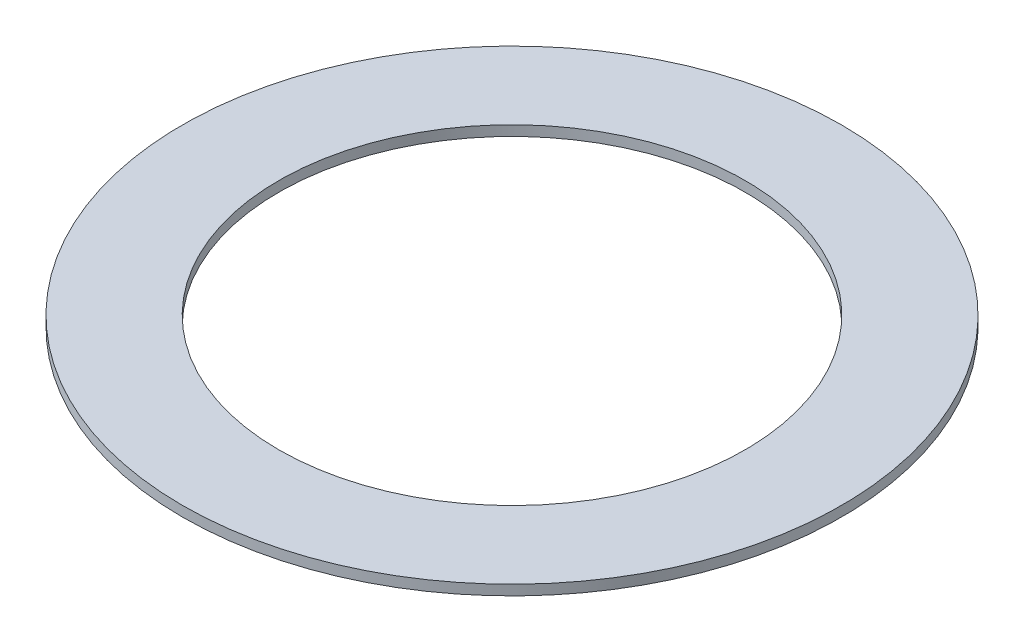
SolidWorks part; units mm, degrees
ref_plane "Alzado" through (0, 0, 0) normal (0, 0, 1) x (1, 0, 0)
ref_plane "Planta" through (0, 0, 0) normal (0, 1, 0) x (1, 0, 0)
ref_plane "Vista lateral" through (0, 0, 0) normal (1, 0, 0) x (0, 0, -1)
sketch "Sketch1" plane through (0, 0, 0) normal (0, 1, 0) x (1, 0, 0)
  circle A0 centre (0, 0) radius 32.5
  circle A1 centre (0, 0) radius 23
  dimension "D1" = 46
  dimension "D2" = 65
extrude "Extrude1" add sketch "Sketch1" along normal blind 1
